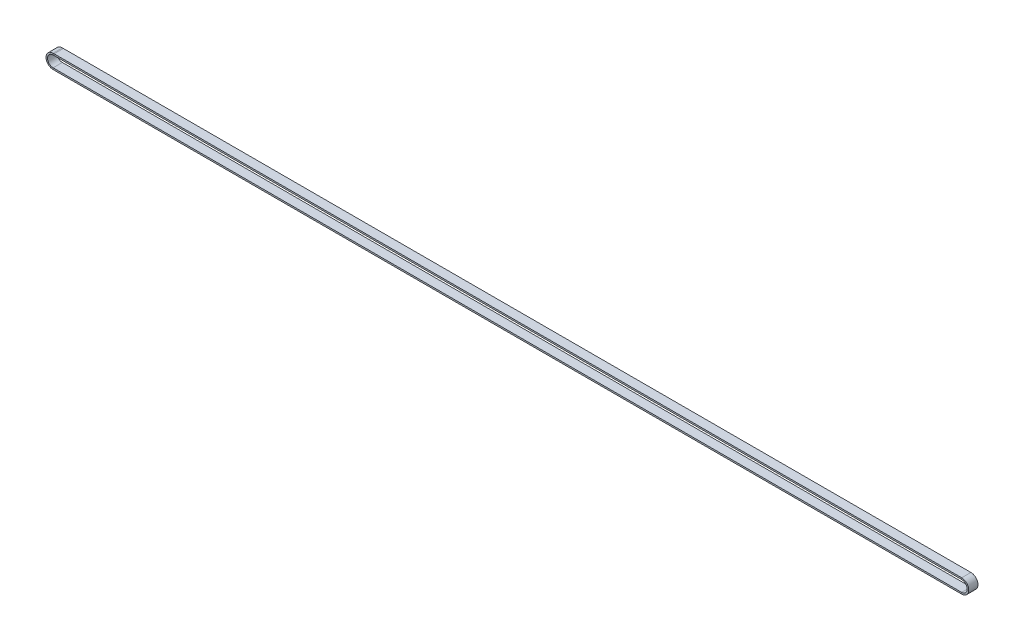
SolidWorks part; units mm, degrees
ref_plane "Front Plane" through (0, 0, 0) normal (0, 0, 1) x (1, 0, 0)
ref_plane "Top Plane" through (0, 0, 0) normal (0, 1, 0) x (1, 0, 0)
ref_plane "Right Plane" through (0, 0, 0) normal (1, 0, 0) x (0, 0, -1)
sketch "Sketch2" plane through (0, 0, -150.4834) normal (0, 0, 1) x (1, 0, 0)
  line L0 (0, 0) -> (1, 0) construction
  line L1 (0, 0) -> (0, 1) construction
  line L2 (-1, 148.3793) -> (883.5206, 148.3793)
  line L3 (883.5206, 134.5793) -> (-1, 134.5793)
  arc A0 (-1, 134.5793) -> (-1, 148.3793) centre (-1, 141.4793) cw
  arc A1 (883.5206, 148.3793) -> (883.5206, 134.5793) centre (883.5206, 141.4793) cw
sketch "Sketch3" plane through (0, 0, 0) normal (1, 0, 0) x (0, 0, -1)
  line L1 (150.4834, 146.8793) -> (141.4834, 146.8793)
  line L2 (150.4834, 146.8793) -> (150.4834, 148.3793)
  line L3 (150.4834, 148.3793) -> (141.4834, 148.3793)
  line L4 (141.4834, 146.8793) -> (141.4834, 148.3793)
  dimension "D1" = 9
  dimension "D2" = 1.5
sweep "Sweep1" add profiles "Sketch3" path "Sketch2"
